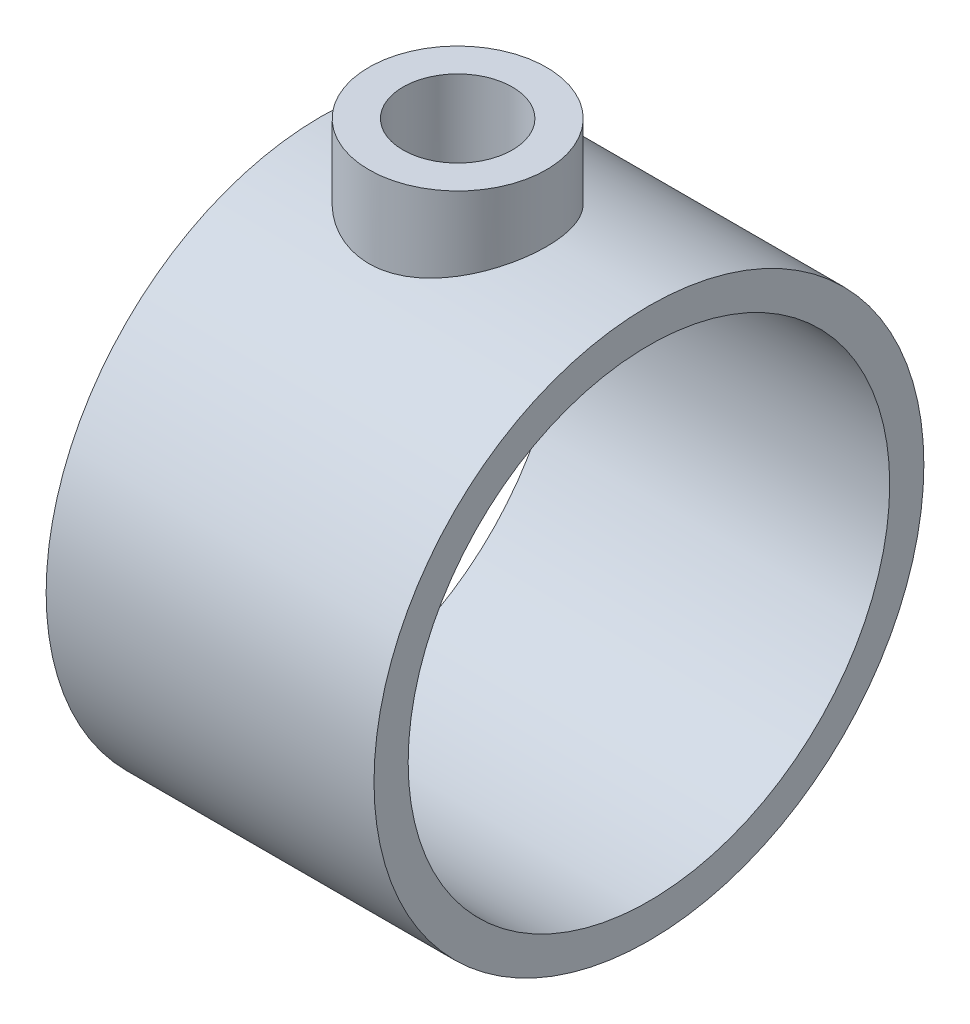
SolidWorks part; units mm, degrees
other "标注1"
sketch "草图8" plane through (-2.7147, -6.8585, 6.8585) normal (-0.2235, -0.0225, 0.9745) x (-0.1799, 0.9835, -0.0185)
ref_plane "前视基准面" through (0, 0, 0) normal (0, 0, 1) x (1, 0, 0)
ref_plane "上视基准面" through (0, 0, 0) normal (0, 1, 0) x (1, 0, 0)
ref_plane "右视基准面" through (0, 0, 0) normal (1, 0, 0) x (0, 0, -1)
sketch "草图1" plane through (0, 0, 0) normal (0, 0, 1) x (1, 0, 0)
  line L0 (3.3809, 3.525) -> (4.3576, 3.525)
  line L4 (7.3809, 4.025) -> (3.3809, 4.025)
  line L5 (3.3809, 4.025) -> (3.3809, 3.525)
  line L10 (4.3576, 3.525) -> (5.4612, 3.525) construction
  line L12 (0, 0) -> (8.3011, 0) construction
  line L20 (4.7691, 3.525) -> (8.1809, 3.525)
  line L22 (4.3576, 3.525) -> (4.7691, 3.525)
  line L24 (7.3809, 4.025) -> (7.3502, 4.025) construction
  line L27 (8.1809, 4.025) -> (8.1809, 3.525)
  line L28 (7.3809, 4.025) -> (8.1809, 4.025)
  dimension "D1" = 0.8
  dimension "D2" = 3.525
  dimension "D3" = 0.5
  dimension "D4" = 4
revolve "旋转1" add sketch "草图1" angle 360 about L12
ref_plane "基准面1" through (0, 5, 0) normal (0, 1, 0) x (1, 0, 0)
sketch "草图10" plane through (0, 5, 0) normal (0, 1, 0) x (1, 0, 0)
  line L0 (3.3809, 4.025) -> (3.3809, -4.025) construction
  circle A0 centre (5.3809, 0) radius 1.3
  dimension "D1" = 2.6
  dimension "D2" = 2
extrude "凸台-拉伸1" add sketch "草图10" against normal blind 1.3
sketch "草图11" plane through (0, 5, 0) normal (0, 1, 0) x (1, 0, 0)
  circle A0 centre (5.3809, 0) radius 0.8
  dimension "D1" = 1.6
extrude "切除-拉伸2" cut sketch "草图11" against normal mid plane 11.3
